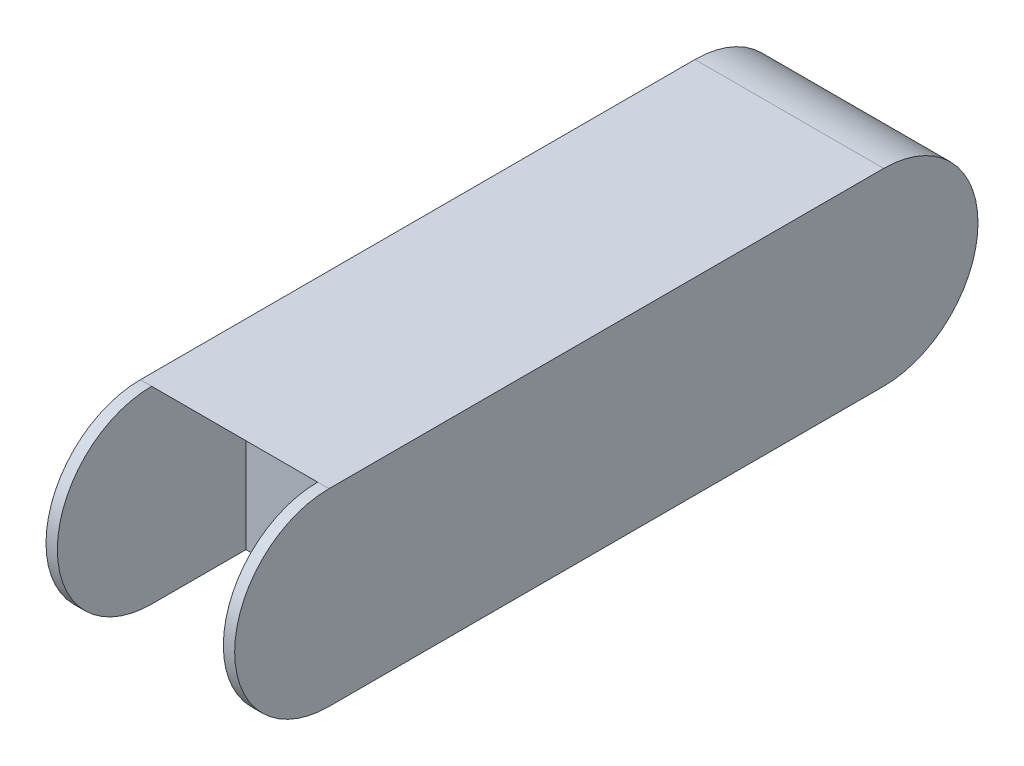
SolidWorks part; units mm, degrees
ref_plane "Front Plane" through (0, 0, 0) normal (0, 0, 1) x (1, 0, 0)
ref_plane "Top Plane" through (0, 0, 0) normal (0, 1, 0) x (1, 0, 0)
ref_plane "Right Plane" through (0, 0, 0) normal (1, 0, 0) x (0, 0, -1)
sketch "Sketch1" plane through (0, 0, 0) normal (1, 0, 0) x (0, 0, -1)
  line L1 (0, 0) -> (0.147, 0)
  line L3 (0, 0.05) -> (0.147, 0.05)
  arc A0 (0, 0) -> (0, 0.05) centre (0, 0.025) ccw
  arc A1 (0.147, 0) -> (0.147, 0.05) centre (0.147, 0.025) ccw
  dimension "D3" = 0.05
  dimension "D4" = 0.05
  dimension "D1" = 0.147
  dimension "D2" = 0.05
extrude "Boss-Extrude1" add sketch "Sketch1" along normal blind 0.05
sketch "Sketch2" plane through (0.05, 0, 0) normal (1, 0, 0) x (0, 0, -1)
  line L1 (0.025, 0.025) -> (0, 0.025)
  line L2 (0.025, 0.025) -> (0.025, 0)
  line L3 (0.025, 0) -> (0, 0)
  line L4 (0, 0.025) -> (0, 0)
  arc A0 (0, 0) -> (0, 0.05) centre (0, 0.025) ccw construction
extrude "Cut-Extrude1" cut sketch "Sketch2" against normal blind 0.05
sketch "Sketch4" plane through (0.05, 0, 0) normal (1, 0, 0) x (0, 0, -1)
  circle A0 centre (0, 0.025) radius 0.025
  dimension "D2" = 0.05
  dimension "D1" = 0.025
extrude "Boss-Extrude2" add sketch "Sketch4" against normal blind 0.003 contours A0
sketch "Sketch5" plane through (0, 0, 0) normal (-1, 0, 0) x (0, 0, 1)
  circle A0 centre (0, 0.025) radius 0.025
extrude "Boss-Extrude3" add sketch "Sketch5" against normal blind 0.003
sketch "Sketch6" plane through (0, 0, 0) normal (-1, 0, 0) x (0, 0, 1)
  line L1 (-0.025, 0.025) -> (0, 0.025)
  line L2 (-0.025, 0.025) -> (-0.025, 0)
  line L3 (-0.025, 0) -> (0, 0)
  line L4 (0, 0.025) -> (0, 0)
extrude "Boss-Extrude4" add sketch "Sketch6" against normal blind 0.003
sketch "Sketch7" plane through (0.05, 0, 0) normal (1, 0, 0) x (0, 0, -1)
  line L1 (0.025, 0.025) -> (0, 0.025)
  line L2 (0.025, 0.025) -> (0.025, 0)
  line L3 (0.025, 0) -> (0, 0)
  line L4 (0, 0.025) -> (0, 0)
extrude "Boss-Extrude5" add sketch "Sketch7" against normal blind 0.003
